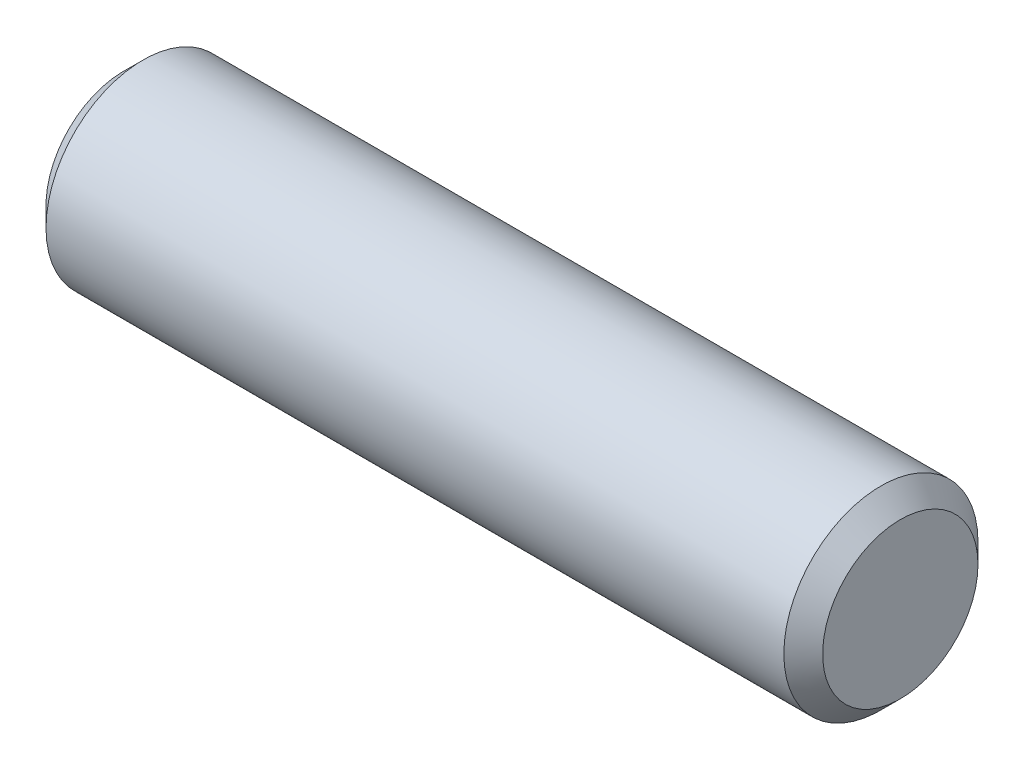
SolidWorks part; units mm, degrees
material "Alloy Steel"
ref_plane "Front" through (0, 0, 0) normal (0, 0, 1) x (1, 0, 0)
ref_plane "Top" through (0, 0, 0) normal (0, 1, 0) x (1, 0, 0)
ref_plane "Right" through (0, 0, 0) normal (1, 0, 0) x (0, 0, -1)
sketch "Sketch1" plane through (0, 0, 0) normal (0, 0, 1) x (1, 0, 0)
  line L0 (-6.35, 0) -> (6.35, 0) construction
  line L1 (6.35, 1.5875) -> (6.35, -1.5875) construction
  line L2 (-6.35, 1.5875) -> (-6.35, -1.5875) construction
  dimension "Length" = 12.7
  dimension "Diameter" = 3.175
sketch "Sketch2" plane through (0, 0, 0) normal (1, 0, 0) x (0, 0, -1)
  circle A0 centre (0, 0) radius 1.5875
extrude "Extrude1" add sketch "Sketch2" against normal up to vertex (6.35 mm away) and the other way up to vertex (6.35 mm away) up to point (-6.35, 1.5875, 0) other way up to point (6.35, 1.5875, 0)
chamfer "Chamfer1" distance 0.3175 angle 45 2 edges at (6.35, 0, -1.5875) (-6.35, 0, -1.5875)
equation "\"D1@Chamfer1\" = \"Diameter@Sketch1\"*.1"
